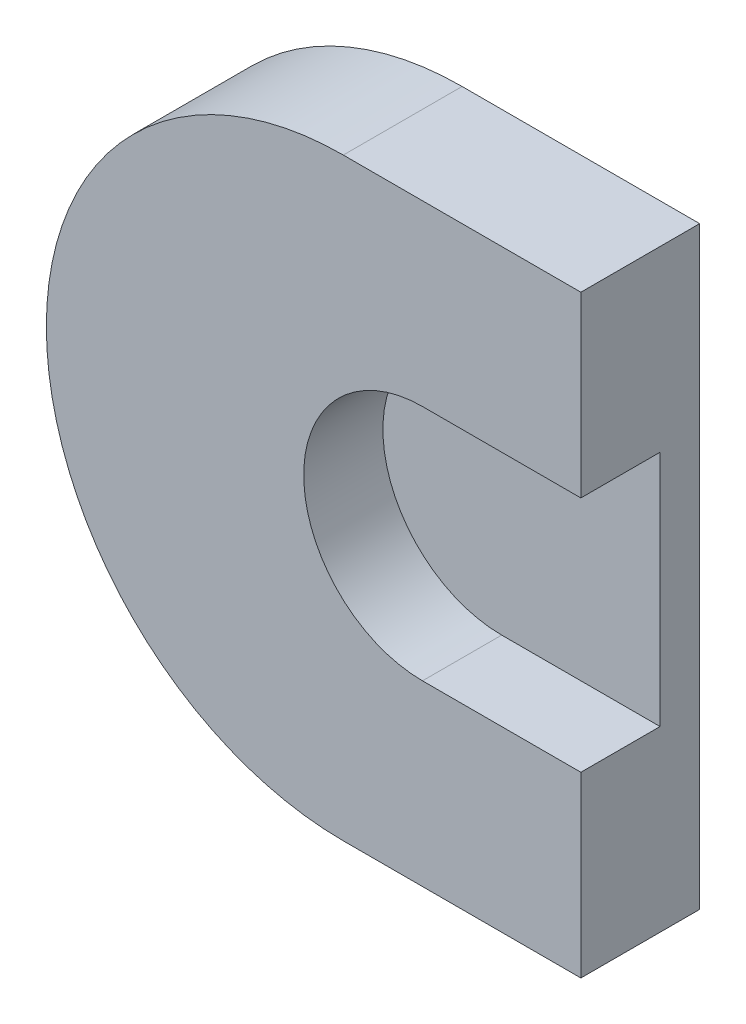
SolidWorks part; units mm, degrees
ref_plane "Спереди" through (0, 0, 0) normal (0, 0, 1) x (1, 0, 0)
ref_plane "Сверху" through (0, 0, 0) normal (0, 1, 0) x (1, 0, 0)
ref_plane "Справа" through (0, 0, 0) normal (1, 0, 0) x (0, 0, -1)
sketch "Эскиз1" plane through (0, 0, 0) normal (0, 0, 1) x (1, 0, 0)
  line L0 (0, 7.5) -> (6, 7.5)
  line L1 (6, 7.5) -> (6, -7.5)
  line L2 (6, -7.5) -> (0, -7.5)
  arc A0 (0, 7.5) -> (0, -7.5) centre (0, 0) ccw
  dimension "D1" = 15
  dimension "D2" = 6
extrude "Бобышка-Вытянуть1" add sketch "Эскиз1" along normal blind 3
sketch "Эскиз2" plane through (0, 0, 3) normal (0, 0, 1) x (1, 0, 0)
  line L0 (6, 0) -> (2, 0) construction
  line L1 (6, -7.5) -> (6, 7.5) construction
  line L2 (6, -3) -> (2, -3)
  line L3 (6, 3) -> (2, 3)
  arc A0 (6, -3) -> (6, 3) centre (6, 0) ccw
  arc A1 (2, 3) -> (2, -3) centre (2, 0) ccw
  point P5 (4, 0)
  dimension "D1" = 3
  dimension "D2" = 4
extrude "Вырез-Вытянуть1" cut sketch "Эскиз2" against normal blind 2
